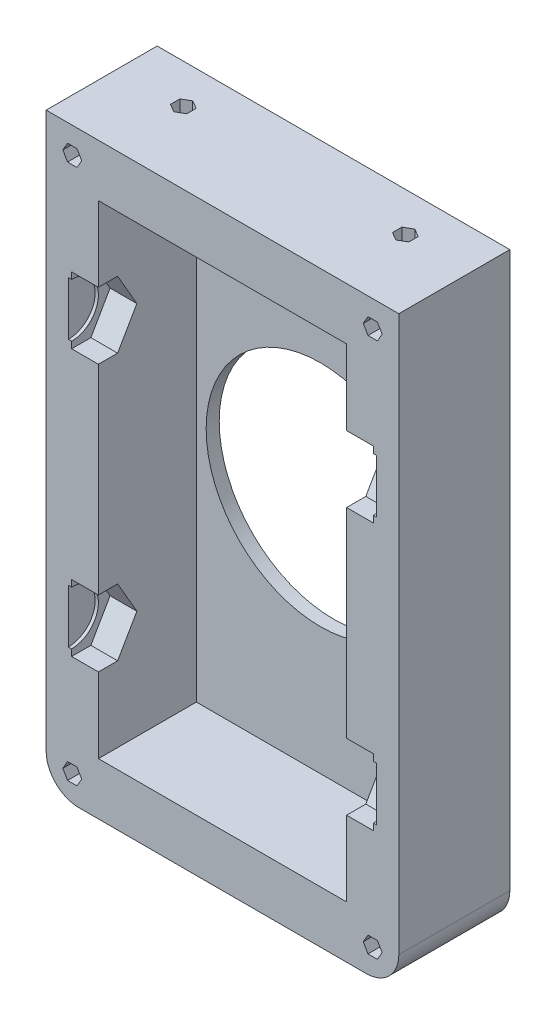
SolidWorks part; units mm, degrees
ref_plane "Front Plane" through (0, 0, 0) normal (0, 0, 1) x (1, 0, 0)
ref_plane "Top Plane" through (0, 0, 0) normal (0, 1, 0) x (1, 0, 0)
ref_plane "Right Plane" through (0, 0, 0) normal (1, 0, 0) x (0, 0, -1)
sketch "Sketch1" plane through (0, 0, 0) normal (0, 0, 1) x (1, 0, 0)
  line L1 (0, 0) -> (54, 0)
  line L2 (0, 0) -> (0, 90)
  line L3 (0, 90) -> (54, 90)
  line L4 (54, 0) -> (54, 90)
  line L5 (8, 82) -> (46, 82)
  line L6 (8, 82) -> (8, 8)
  line L7 (8, 8) -> (46, 8)
  line L8 (46, 82) -> (46, 8)
  dimension "D1" = 90
  dimension "D2" = 54
  dimension "D3" = 8
  dimension "D4" = 8
  dimension "D5" = 8
  dimension "D6" = 8
extrude "Boss-Extrude1" add sketch "Sketch1" along normal blind 30
sketch "Sketch2" plane through (46, 0, 0) normal (-1, 0, 0) x (0, 0, 1)
  line L0 (15, 82) -> (15, 8) construction
  line L1 (20.889, 65.4) -> (17.9445, 70.5)
  line L2 (17.9445, 70.5) -> (12.0555, 70.5)
  line L3 (12.0555, 70.5) -> (9.111, 65.4)
  line L4 (9.111, 65.4) -> (12.0555, 60.3)
  line L5 (12.0555, 60.3) -> (17.9445, 60.3)
  line L6 (17.9445, 60.3) -> (20.889, 65.4)
  line L8 (0, 8) -> (0, 82) construction
  line L10 (20.889, 24.6) -> (17.9445, 29.7)
  line L11 (17.9445, 29.7) -> (12.0555, 29.7)
  line L12 (12.0555, 29.7) -> (9.111, 24.6)
  line L13 (9.111, 24.6) -> (12.0555, 19.5)
  line L14 (12.0555, 19.5) -> (17.9445, 19.5)
  line L15 (17.9445, 19.5) -> (20.889, 24.6)
  line L16 (12.0555, 70.5) -> (17.9445, 60.3) construction
  line L17 (17.9445, 19.5) -> (12.0555, 29.7) construction
  line L18 (12.0555, 60.3) -> (17.9445, 70.5) construction
  line L19 (30, 82) -> (0, 82) construction
  line L20 (30, 8) -> (0, 8) construction
  line L21 (0, 45) -> (30, 45) construction
  line L22 (30, 8) -> (30, 82) construction
  line L23 (17.9445, 29.7) -> (12.0555, 19.5) construction
  circle A0 centre (15, 65.4) radius 5.1 construction
  circle A1 centre (15, 24.6) radius 5.1 construction
  point P28 (15, 45)
  dimension "D1" = 20.4
  dimension "D2" = 15
  dimension "D3" = 10.2
  dimension "D4" = 20.4
  dimension "D5" = 15
  dimension "D6" = 10.2
extrude "Cut-Extrude1" cut sketch "Sketch2" against normal blind 4.1
sketch "Sketch5" plane through (50.1, 0, 0) normal (-1, 0, 0) x (0, 0, 1)
  line L0 (12.0555, 70.5) -> (17.9445, 60.3) construction
  line L1 (12.0555, 60.3) -> (17.9445, 70.5) construction
  line L2 (12.0555, 19.5) -> (17.9445, 29.7) construction
  line L3 (17.9445, 19.5) -> (12.0555, 29.7) construction
  circle A0 centre (15, 65.4) radius 4.1
  circle A1 centre (15, 24.6) radius 4.1
  dimension "D1" = 8.2
  dimension "D2" = 8.2
extrude "Cut-Extrude2" cut sketch "Sketch5" against normal blind 0.5
sketch "Sketch6" plane through (8, 0, 0) normal (1, 0, 0) x (0, 0, -1)
  line L1 (-9.111, 65.4) -> (-12.0555, 70.5)
  line L2 (-12.0555, 70.5) -> (-17.9445, 70.5)
  line L3 (-17.9445, 70.5) -> (-20.889, 65.4)
  line L4 (-20.889, 65.4) -> (-17.9445, 60.3)
  line L5 (-17.9445, 60.3) -> (-12.0555, 60.3)
  line L6 (-12.0555, 60.3) -> (-9.111, 65.4)
  line L7 (-9.111, 24.6) -> (-12.0555, 29.7)
  line L8 (-12.0555, 29.7) -> (-17.9445, 29.7)
  line L9 (-17.9445, 29.7) -> (-20.889, 24.6)
  line L10 (-20.889, 24.6) -> (-17.9445, 19.5)
  line L11 (-17.9445, 19.5) -> (-12.0555, 19.5)
  line L12 (-12.0555, 19.5) -> (-9.111, 24.6)
  line L13 (-30, 82) -> (-30, 8) construction
  line L15 (-30, 45) -> (0, 45) construction
  line L16 (0, 82) -> (0, 8) construction
  circle A0 centre (-15, 65.4) radius 5.1 construction
  circle A1 centre (-15, 24.6) radius 5.1 construction
  dimension "D1" = 20.4
  dimension "D2" = 15
  dimension "D3" = 20.4
  dimension "D4" = 15
  dimension "D5" = 10.2
  dimension "D6" = 10.2
extrude "Cut-Extrude3" cut sketch "Sketch6" against normal blind 4.1
sketch "Sketch7" plane through (3.9, 0, 0) normal (1, 0, 0) x (0, 0, -1)
  line L0 (-12.0555, 29.7) -> (-17.9445, 19.5) construction
  line L3 (-12.0555, 70.5) -> (-17.9445, 60.3) construction
  circle A0 centre (-15, 65.4) radius 4.1
  circle A1 centre (-15, 24.6) radius 4.1
  point P16 (-15, 65.4)
  point P17 (-15, 24.6)
  dimension "D1" = 8.2
  dimension "D5" = 0
extrude "Cut-Extrude4" cut sketch "Sketch7" against normal blind 0.5
sketch "Sketch8" plane through (0, 0, 30) normal (0, 0, 1) x (1, 0, 0)
  line L1 (0, 90) -> (54, 90)
  line L2 (0, 90) -> (0, 0)
  line L3 (0, 0) -> (54, 0)
  line L4 (54, 90) -> (54, 0)
extrude "Boss-Extrude2" add sketch "Sketch8" along normal blind 2
sketch "Sketch9" plane through (0, 0, 0) normal (0, 0, -1) x (-1, 0, 0)
  line L1 (-54, 90) -> (0, 90)
  line L2 (-54, 90) -> (-54, 0)
  line L3 (-54, 0) -> (0, 0)
  line L4 (0, 90) -> (0, 0)
extrude "Boss-Extrude3" add sketch "Sketch9" along normal blind 2
sketch "Sketch10" plane through (0, 0, 32) normal (0, 0, 1) x (1, 0, 0)
  line L1 (0, 90) -> (54, 90)
  line L2 (0, 90) -> (0, 0)
  line L3 (0, 0) -> (54, 0)
  line L4 (54, 90) -> (54, 0)
extrude "Cut-Extrude5" cut sketch "Sketch10" against normal blind 17
sketch "Sketch11" plane through (0, 0, 0) normal (0, 0, 1) x (1, 0, 0)
  line L2 (54, 45) -> (0, 45) construction
  line L4 (54, 90) -> (54, 0) construction
  line L5 (0, 0) -> (0, 90) construction
  circle A0 centre (27, 45) radius 17.5
  point P6 (27, 45)
  dimension "D1" = 35
extrude "Cut-Extrude6" cut sketch "Sketch11" against normal through all
sketch "Sketch12" plane through (0, 0, 15) normal (0, 0, 1) x (1, 0, 0)
  line L0 (54, 0) -> (54, 90) construction
  line L1 (5.4434, 86) -> (4.7217, 87.25)
  line L2 (4.7217, 87.25) -> (3.2783, 87.25)
  line L3 (3.2783, 87.25) -> (2.5566, 86)
  line L4 (2.5566, 86) -> (3.2783, 84.75)
  line L5 (3.2783, 84.75) -> (4.7217, 84.75)
  line L6 (4.7217, 84.75) -> (5.4434, 86)
  line L7 (51.4434, 86) -> (50.7217, 87.25)
  line L8 (50.7217, 87.25) -> (49.2783, 87.25)
  line L9 (49.2783, 87.25) -> (48.5566, 86)
  line L10 (48.5566, 86) -> (49.2783, 84.75)
  line L11 (49.2783, 84.75) -> (50.7217, 84.75)
  line L12 (50.7217, 84.75) -> (51.4434, 86)
  line L14 (54, 90) -> (0, 90) construction
  line L15 (0, 90) -> (0, 0) construction
  line L16 (3.2783, 2.75) -> (4.7217, 2.75)
  line L17 (2.5566, 4) -> (3.2783, 2.75)
  line L18 (3.2783, 5.25) -> (2.5566, 4)
  line L19 (4.7217, 5.25) -> (3.2783, 5.25)
  line L20 (5.4434, 4) -> (4.7217, 5.25)
  line L21 (4.7217, 2.75) -> (5.4434, 4)
  line L22 (50.7217, 5.25) -> (49.2783, 5.25)
  line L23 (49.2783, 5.25) -> (48.5566, 4)
  line L24 (48.5566, 4) -> (49.2783, 2.75)
  line L25 (49.2783, 2.75) -> (50.7217, 2.75)
  line L26 (50.7217, 2.75) -> (51.4434, 4)
  line L27 (51.4434, 4) -> (50.7217, 5.25)
  circle A0 centre (4, 86) radius 1.25 construction
  circle A1 centre (50, 86) radius 1.25 construction
  dimension "D1" = 2.5
  dimension "D2" = 2.5
  dimension "D3" = 4
  dimension "D4" = 4
  dimension "D5" = 4
  dimension "D6" = 4
  dimension "D7" = 2
extrude "Cut-Extrude7" cut sketch "Sketch12" against normal through all
sketch "Sketch13" plane through (0, 90, 0) normal (0, 1, 0) x (1, 0, 0)
  line L0 (54, -15) -> (0, -15) construction
  line L1 (10, -2.5566) -> (8.75, -3.2783)
  line L2 (8.75, -3.2783) -> (8.75, -4.7217)
  line L3 (8.75, -4.7217) -> (10, -5.4434)
  line L4 (10, -5.4434) -> (11.25, -4.7217)
  line L5 (11.25, -4.7217) -> (11.25, -3.2783)
  line L6 (11.25, -3.2783) -> (10, -2.5566)
  line L7 (44, -2.5566) -> (42.75, -3.2783)
  line L8 (42.75, -3.2783) -> (42.75, -4.7217)
  line L9 (42.75, -4.7217) -> (44, -5.4434)
  line L10 (44, -5.4434) -> (45.25, -4.7217)
  line L11 (45.25, -4.7217) -> (45.25, -3.2783)
  line L12 (45.25, -3.2783) -> (44, -2.5566)
  line L14 (54, -15) -> (54, 2) construction
  line L15 (0, -15) -> (0, 2) construction
  circle A0 centre (10, -4) radius 1.25 construction
  circle A1 centre (44, -4) radius 1.25 construction
  dimension "D1" = 11
  dimension "D2" = 11
  dimension "D3" = 10
  dimension "D4" = 10
  dimension "D5" = 2.5
  dimension "D6" = 2.5
extrude "Cut-Extrude8" cut sketch "Sketch13" against normal blind 5
fillet "Fillet1" radius 5 2 edges at (54, 0, 6.5) (0, 0, 6.5)
